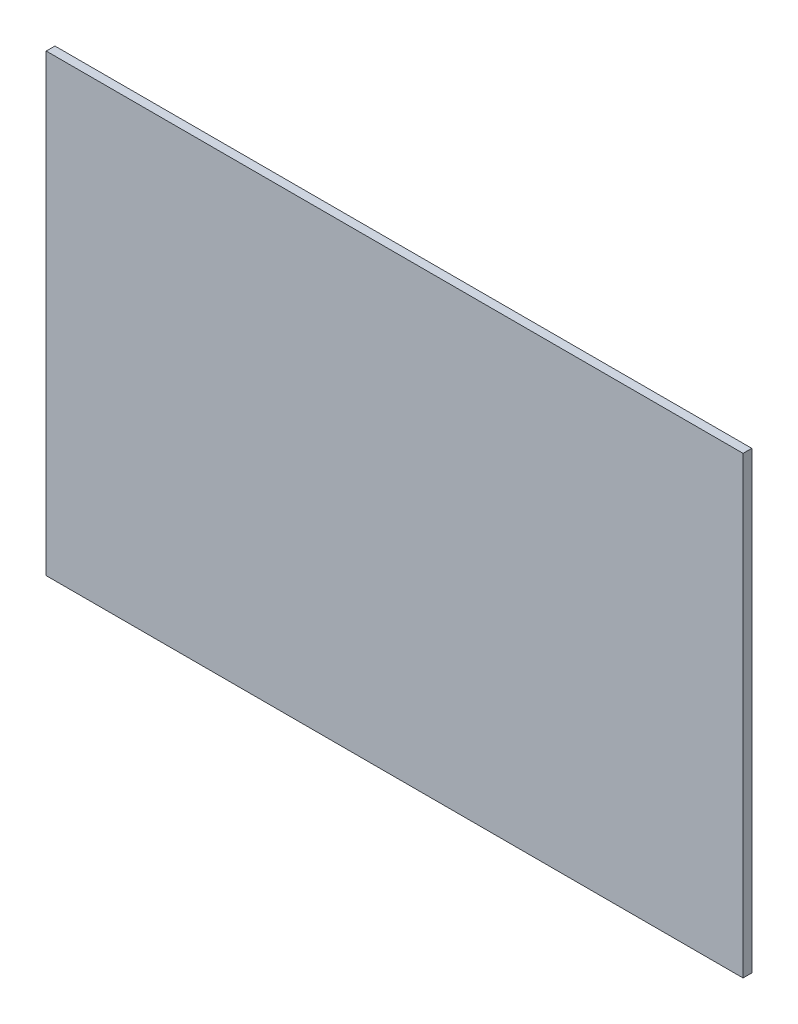
SolidWorks part; units mm, degrees
material "PBT General Purpose"
ref_plane "Front Plane" through (0, 0, 0) normal (0, 0, 1) x (1, 0, 0)
ref_plane "Top Plane" through (0, 0, 0) normal (0, 1, 0) x (1, 0, 0)
ref_plane "Right Plane" through (0, 0, 0) normal (1, 0, 0) x (0, 0, -1)
sketch "Sketch1" plane through (0, 0, 0) normal (0, 0, 1) x (1, 0, 0)
  line L1 (0, 0) -> (400, 0)
  line L2 (0, 0) -> (0, -260.8)
  line L3 (0, -260.8) -> (400, -260.8)
  line L4 (400, 0) -> (400, -260.8)
  dimension "D1" = 400
  dimension "D2" = 260.8
extrude "Boss-Extrude1" add sketch "Sketch1" along normal blind 5
